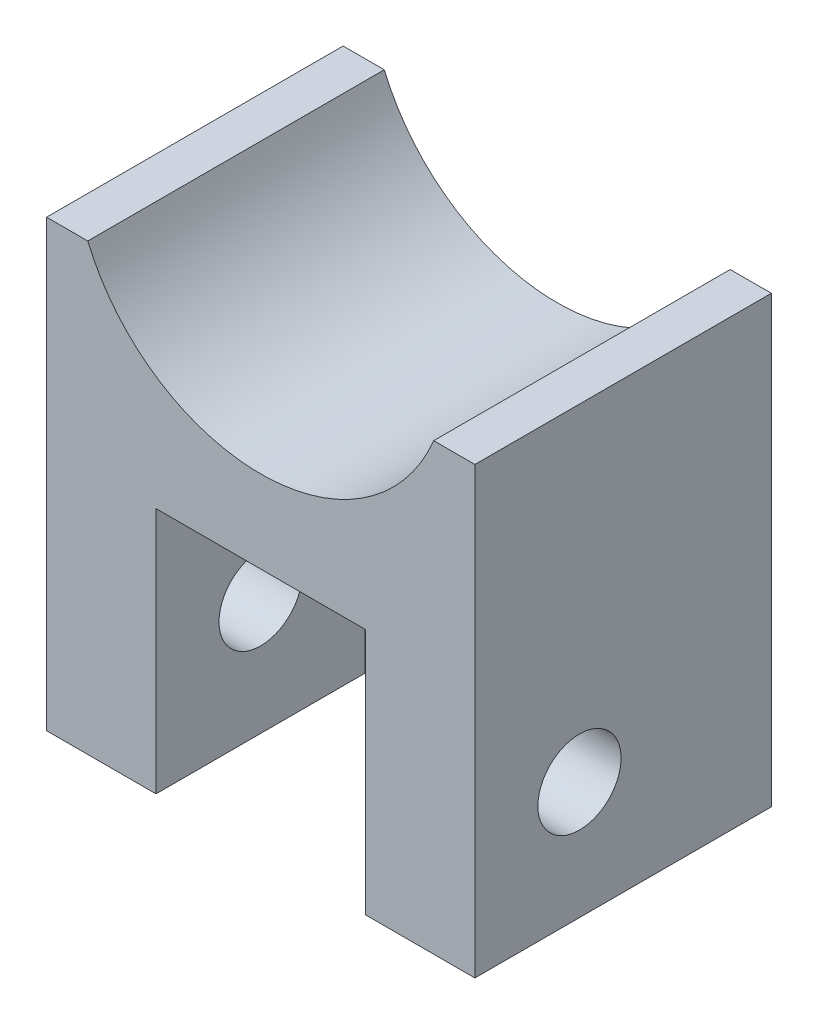
SolidWorks part; units mm, degrees
ref_plane "Plan de face" through (0, 0, 0) normal (0, 0, 1) x (1, 0, 0)
ref_plane "Plan de dessus" through (0, 0, 0) normal (0, 1, 0) x (1, 0, 0)
ref_plane "Plan de droite" through (0, 0, 0) normal (1, 0, 0) x (0, 0, -1)
sketch "Esquisse1" plane through (0, 0, 0) normal (0, 0, 1) x (1, 0, 0)
  line L0 (0, 0) -> (26, 0)
  line L1 (13, 31.375) -> (13, 0) construction
  line L2 (0, 0) -> (0, 27)
  line L3 (-9.2677, 20) -> (34.2727, 20) construction
  line L4 (0, 27) -> (2.5, 27)
  line L5 (26, 27) -> (23.5, 27)
  line L6 (26, 0) -> (26, 27)
  arc A0 (2.5, 27) -> (23.5, 27) centre (13, 31.375) ccw
  point P11 (13, 20)
  dimension "D3" = 13
  dimension "D4" = 2.5
  dimension "D2" = 27
  dimension "D1" = 20
extrude "Boss.-Extru.1" add sketch "Esquisse1" along normal blind 18
sketch "Esquisse2" plane through (0, 0, 18) normal (0, 0, 1) x (1, 0, 0)
  line L1 (6.64, 15) -> (19.36, 15)
  line L2 (6.64, 15) -> (6.64, 0)
  line L3 (6.64, 0) -> (19.36, 0)
  line L4 (19.36, 15) -> (19.36, 0)
  line L5 (6.64, 15) -> (19.36, 0) construction
  line L6 (6.64, 0) -> (19.36, 15) construction
  line L7 (0, 27) -> (0, 0) construction
  line L8 (26, 0) -> (26, 27) construction
  line L9 (13, 25.1696) -> (13, -2.2391) construction
  line L12 (0, 0) -> (26, 0) construction
  point P0 (13, 7.5)
  dimension "D1" = 15
  dimension "D2" = 12.72
extrude "Enlèv. mat.-Extru.1" cut sketch "Esquisse2" against normal blind 12.7
sketch "Esquisse3" plane through (0, 0, 0) normal (-1, 0, 0) x (0, 0, 1)
  line L0 (5.3, 0) -> (5.3, 15) construction
  line L2 (5.3, 15) -> (18, 15) construction
  line L3 (18, 27) -> (18, 0) construction
  line L4 (5.3, 15) -> (18, 15) construction
  line L5 (5.3, 15) -> (5.3, 0) construction
  line L6 (11.65, 15) -> (11.65, 0) construction
  line L7 (18, 0) -> (0, 0) construction
  circle A0 centre (11.65, 7.13) radius 2.525
  point P15 (0, 0)
  point P16 (0, 0)
  point P19 (0, 0)
  point P20 (0, 0)
  dimension "D1" = 5.05
  dimension "D2" = 7.13
extrude "Enlèv. mat.-Extru.2" cut sketch "Esquisse3" against normal through all
equation "\"5.0.5mm\"=5.2"
